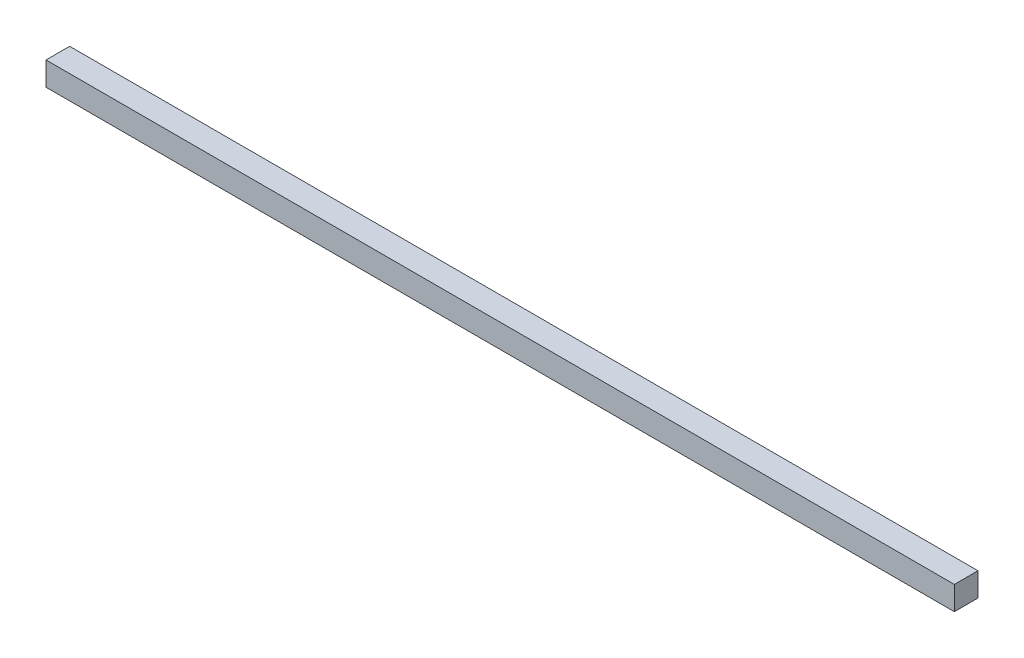
SolidWorks part; units mm, degrees
ref_plane "Front Plane" through (0, 0, 0) normal (0, 0, 1) x (1, 0, 0)
ref_plane "Top Plane" through (0, 0, 0) normal (0, 1, 0) x (1, 0, 0)
ref_plane "Right Plane" through (0, 0, 0) normal (1, 0, 0) x (0, 0, -1)
sketch "Sketch1" plane through (0, 0, 0) normal (0, 1, 0) x (1, 0, 0)
  line L1 (0, 0) -> (975.5374, 0)
  line L2 (0, 0) -> (0, 25.4)
  line L3 (0, 25.4) -> (975.5374, 25.4)
  line L4 (975.5374, 0) -> (975.5374, 25.4)
  dimension "D1" = 975.868
  dimension "D2" = 25.4
extrude "Boss-Extrude1" add sketch "Sketch1" along normal blind 25.4
